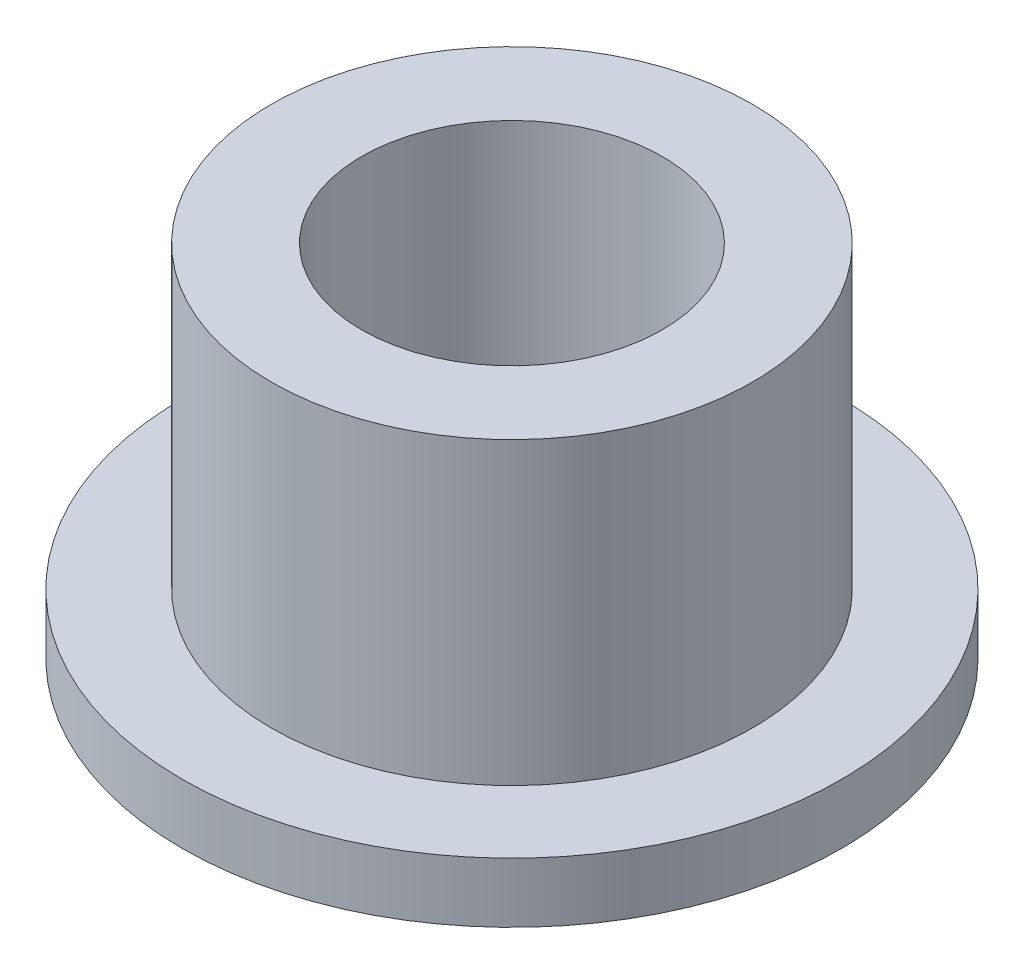
SolidWorks part; units mm, degrees
material "Tin Bearing Bronze"
ref_plane "Front" through (0, 0, 0) normal (0, 0, 1) x (1, 0, 0)
ref_plane "Top" through (0, 0, 0) normal (0, 1, 0) x (1, 0, 0)
ref_plane "Right" through (0, 0, 0) normal (1, 0, 0) x (0, 0, -1)
sketch "Sketch1" plane through (0, 0, 0) normal (0, 1, 0) x (1, 0, 0)
  circle A0 centre (0, 0) radius 3.9815
  circle A1 centre (0, 0) radius 6.3754
  circle A2 centre (0, 0) radius 8.7312
  dimension "ID" = 7.9629
  dimension "OD" = 12.7508
  dimension "FlangeOD" = 17.4625
sketch "Sketch2" plane through (0, 0, 0) normal (0, 1, 0) x (1, 0, 0)
  circle A0 centre (0, 0) radius 3.9815 construction
  circle A1 centre (0, 0) radius 6.3754 construction
  circle A2 centre (0, 0) radius 3.9815
  circle A3 centre (0, 0) radius 6.3754
extrude "Boss-Extrude1" add sketch "Sketch2" along normal blind 9.525
sketch "Sketch3" plane through (0, 0, 0) normal (0, 1, 0) x (1, 0, 0)
  circle A0 centre (0, 0) radius 8.7312 construction
  circle A1 centre (0, 0) radius 6.3754 construction
  circle A2 centre (0, 0) radius 8.7312
  circle A3 centre (0, 0) radius 6.3754
extrude "Boss-Extrude2" add sketch "Sketch3" along normal blind 1.5875
